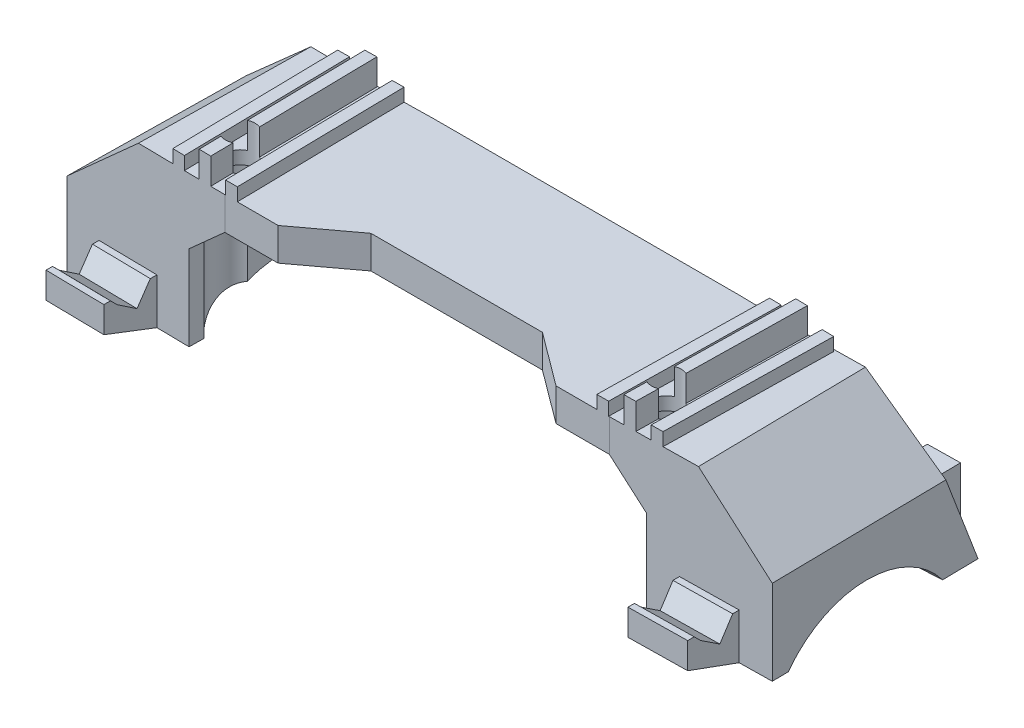
SolidWorks part; units mm, degrees
ref_plane "Front Plane" through (0, 0, 0) normal (0, 0, 1) x (1, 0, 0)
ref_plane "Top Plane" through (0, 0, 0) normal (0, 1, 0) x (1, 0, 0)
ref_plane "Right Plane" through (0, 0, 0) normal (1, 0, 0) x (0, 0, -1)
sketch "Sketch1" plane through (0, 0, 0) normal (0, 1, 0) x (1, 0, 0)
  line L0 (-41.9971, 0) -> (-23, 0.3316)
  line L1 (-23, 0.3316) -> (-23.4773, 27.6774)
  line L2 (-23.4773, 27.6774) -> (-42.4744, 27.3458)
  line L3 (-42.4744, 27.3458) -> (-41.9971, 0)
  line L4 (0, 0) -> (-41.9971, 0) construction
  dimension "D1" = 1
  dimension "D2" = 19
  dimension "D3" = 27.35
  dimension "D4" = 23
extrude "Boss-Extrude1" add sketch "Sketch1" against normal blind 5
sketch "Sketch2" plane through (0, 0, 0) normal (0, 1, 0) x (1, 0, 0)
  line L0 (-33.3984, 0.1501) -> (-33.8757, 27.4959)
  line L1 (-41.9971, 0) -> (-23, 0.3316) construction
  line L2 (-23.4773, 27.6774) -> (-42.4744, 27.3458) construction
  line L3 (-33.8757, 27.4959) -> (-32.076, 27.5273)
  line L4 (-32.076, 27.5273) -> (-31.5987, 0.1815)
  line L5 (-31.5987, 0.1815) -> (-33.3984, 0.1501)
  point P6 (-32.4986, 0.1658)
  dimension "D1" = 1.8
  dimension "D2" = 0.9
extrude "Boss-Extrude2" add sketch "Sketch2" along normal blind 4
sketch "Sketch3" plane through (0, 0, 0) normal (0, 1, 0) x (1, 0, 0)
  line L0 (-37.9751, 27.4244) -> (-36.1754, 27.4558)
  line L1 (-33.8757, 27.4959) -> (-42.4744, 27.3458) construction
  line L2 (-36.1754, 27.4558) -> (-35.6981, 0.11)
  line L3 (-41.9971, 0) -> (-33.3984, 0.1501) construction
  line L4 (-35.6981, 0.11) -> (-37.4978, 0.0785)
  line L5 (-37.4978, 0.0785) -> (-37.9751, 27.4244)
  line L6 (-33.8757, 27.4959) -> (-33.3984, 0.1501) construction
  dimension "D1" = 1.8
  dimension "D2" = 2.3
extrude "Boss-Extrude3" add sketch "Sketch3" along normal blind 2
sketch "Sketch4" plane through (0, 0, 0) normal (0, 1, 0) x (1, 0, 0)
  line L0 (-29.7764, 27.5675) -> (-27.9766, 27.5989)
  line L1 (-23.4773, 27.6774) -> (-32.076, 27.5273) construction
  line L2 (-27.9766, 27.5989) -> (-27.4993, 0.2531)
  line L3 (-31.5987, 0.1815) -> (-23, 0.3316) construction
  line L4 (-27.4993, 0.2531) -> (-29.299, 0.2216)
  line L5 (-29.299, 0.2216) -> (-29.7764, 27.5675)
  line L6 (-31.5987, 0.1815) -> (-32.076, 27.5273) construction
  dimension "D1" = 2.3
  dimension "D2" = 1.8
extrude "Boss-Extrude4" add sketch "Sketch4" along normal blind 2
sketch "Sketch7" plane through (0, 0, 0) normal (0, 1, 0) x (1, 0, 0)
  line L0 (23, 0.3316) -> (41.9971, 0)
  line L1 (41.9971, 0) -> (42.4744, 27.3458)
  line L2 (42.4744, 27.3458) -> (23.4773, 27.6774)
  line L3 (23.4773, 27.6774) -> (23, 0.3316)
  line L4 (0, 0) -> (41.9971, 0) construction
  line L5 (41.9971, 0) -> (23.0236, -1.3184) construction
  dimension "D1" = 23
  dimension "D2" = 1
  dimension "D3" = 19
  dimension "D4" = 27.35
extrude "Boss-Extrude5" add sketch "Sketch7" against normal blind 5 separate body
sketch "Sketch8" plane through (0, 0, 0) normal (0, -1, 0) x (-1, 0, 0)
  line L0 (-31.5987, 0.1815) -> (-32.076, 27.5273)
  line L1 (-23, 0.3316) -> (-41.9971, 0) construction
  line L2 (-42.4744, 27.3458) -> (-23.4773, 27.6774) construction
  line L3 (-32.076, 27.5273) -> (-33.8757, 27.4959)
  line L4 (-33.8757, 27.4959) -> (-33.3984, 0.1501)
  line L5 (-33.3984, 0.1501) -> (-31.5987, 0.1815)
  point P8 (-32.4986, 0.1658)
  dimension "D1" = 1.8
  dimension "D2" = 0.9
extrude "Boss-Extrude6" add sketch "Sketch8" against normal blind 4
sketch "Sketch9" plane through (0, 0, 0) normal (0, -1, 0) x (-1, 0, 0)
  line L0 (-37.4978, 0.0785) -> (-37.9751, 27.4244)
  line L1 (-23, 0.3316) -> (-41.9971, 0) construction
  line L2 (-37.9751, 27.4244) -> (-36.1754, 27.4558)
  line L3 (-42.4744, 27.3458) -> (-23.4773, 27.6774) construction
  line L4 (-36.1754, 27.4558) -> (-35.6981, 0.11)
  line L5 (-35.6981, 0.11) -> (-37.4978, 0.0785)
  line L8 (-33.8757, 27.4959) -> (-33.3984, 0.1501) construction
  dimension "D1" = 1.8
  dimension "D2" = 2.3
extrude "Boss-Extrude7" add sketch "Sketch9" against normal blind 2
sketch "Sketch10" plane through (0, 0, 0) normal (0, -1, 0) x (-1, 0, 0)
  line L0 (-27.4993, 0.2531) -> (-27.9766, 27.5989)
  line L1 (-23, 0.3316) -> (-41.9971, 0) construction
  line L2 (-42.4744, 27.3458) -> (-23.4773, 27.6774) construction
  line L3 (-27.9766, 27.5989) -> (-29.7764, 27.5675)
  line L4 (-29.7764, 27.5675) -> (-29.299, 0.2216)
  line L5 (-29.299, 0.2216) -> (-27.4993, 0.2531)
  line L7 (-31.5987, 0.1815) -> (-32.076, 27.5273) construction
  dimension "D1" = 2.3
  dimension "D2" = 1.8
extrude "Boss-Extrude8" add sketch "Sketch10" against normal blind 2
sketch "Sketch13" plane through (0, 0, 0) normal (0, 1, 0) x (1, 0, 0)
  line L0 (23, 0.3316) -> (27.4993, 0.2531) construction
  line L1 (-23, 0.3316) -> (-23.4773, 27.6774) construction
  line L2 (23.4773, 27.6774) -> (23, 0.3316) construction
  line L3 (23, 0.3316) -> (23.4773, 27.6774)
  line L4 (23.4773, 27.6774) -> (-23.4773, 27.6774)
  line L5 (-23.4773, 27.6774) -> (-23, 0.3316)
  line L6 (23.4773, 27.6774) -> (23, 0.3316) construction
  line L7 (-23, 0.3316) -> (-13.1267, 7.6774)
  line L8 (-13.1267, 7.6774) -> (13.1267, 7.6774)
  line L9 (13.1267, 7.6774) -> (23, 0.3316)
  dimension "D1" = 20
  dimension "D2" = 10
  dimension "D3" = 10
extrude "Boss-Extrude9" add sketch "Sketch13" against normal up to surface (5 mm away) up to face at (-32.7372, -5, -13.8387)
ref_plane "Plane1" through (0, -10, 0) normal (0, 1, 0) x (1, 0, 0)
sketch "Sketch14" plane through (0, -10, 0) normal (0, 1, 0) x (1, 0, 0)
  line L0 (-53.9977, 2) -> (-35, 1.7031)
  line L1 (-35, 1.7031) -> (-34.5, 33.6992)
  line L2 (-34.5, 33.6992) -> (-53.4977, 33.9961)
  line L3 (-53.4977, 33.9961) -> (-53.9977, 2)
  line L4 (-53.9977, 2) -> (0, 2) construction
  dimension "D1" = 34.5
  dimension "D2" = 19
  dimension "D3" = 32
  dimension "D4" = 2
  dimension "D5" = 35
extrude "Boss-Extrude10" add sketch "Sketch14" against normal blind 13 separate body
sketch "Sketch51" plane through (0.0181, 0, -1.1559) normal (-0.0156, 0, 0.9999) x (0.9999, 0, 0.0156)
  line L0 (-54.0223, -10) -> (-35.0223, -10)
  line L1 (-35.0223, -10) -> (-35.0223, -11)
  line L2 (-35.0223, -23) -> (-35.0223, -10) construction
  line L3 (-35.0223, -11) -> (-54.0223, -10)
  dimension "D1" = 1
ref_plane "Plane6" through (-0.674, -12.8078, -0.0105) normal (0.0526, 0.9986, 0.0008) x (-0.9985, 0.0526, -0.0156)
ref_plane "Plane7" through (-53.7157, 1.4128, -0.8394) normal (0.9995, -0.0263, 0.0156) x (0.0156, -0.0004, -0.9999)
sketch "Sketch15" plane through (-54.2786, -19.9965, -0.8482) normal (0.9995, -0.0263, 0.0156) x (-0.0156, 0, 0.9999)
  line L0 (-1.156, 2.9955) -> (-1.156, -10) construction
  line L2 (-33.156, -10) -> (-1.156, -10) construction
  circle A0 centre (-15.656, 12) radius 15
  dimension "D1" = 14.5
  dimension "D2" = 22
  dimension "D5" = 30
extrude "Cut-Extrude6" cut sketch "Sketch15" against normal up to surface (19.1907 mm away) contours A0
sketch "Sketch16" plane through (-54.0157, 0, -0.8441) normal (-0.9999, 0, -0.0156) x (-0.0156, 0, 0.9999)
  line L0 (-33.156, -23) -> (-28.156, -10)
  line L1 (-33.156, -10) -> (-1.156, -10) construction
  line L2 (-28.156, -10) -> (-33.156, -10)
  line L3 (-33.156, -10) -> (-33.156, -23)
  dimension "D1" = 5
extrude "Cut-Extrude7" cut sketch "Sketch16" against normal up to surface (19 mm away) up to face at (-34.7578, -17.7503, -17.2012)
sketch "Sketch18" plane through (0, -23, 0) normal (0, -1, 0) x (1, 0, 0)
  line L0 (-46.4282, -38.3862) -> (-46.5688, -29.3873)
  line L2 (-46.5688, -29.3873) -> (-41.5695, -29.3091)
  line L3 (-41.5695, -29.3091) -> (-41.4288, -38.308)
  line L4 (-46.4282, -38.3862) -> (-41.4288, -38.308)
  line L5 (-34.5, -33.6992) -> (-53.4977, -33.9961) construction
  line L8 (-34.5921, -27.8049) -> (-34.5, -33.6992) construction
  dimension "D1" = 4.5
  dimension "D2" = 5
  dimension "D3" = 7
  dimension "D4" = 4.5
extrude "Boss-Extrude12" add sketch "Sketch18" against normal blind 7
sketch "Sketch24" plane through (0, -10, 0) normal (0, 1, 0) x (1, 0, 0)
  line L0 (-48.5764, 28.9186) -> (-48.4983, 33.918)
  line L1 (-34.5781, 28.6998) -> (-53.5758, 28.9967) construction
  line L2 (-46.4985, 33.8867) -> (-53.4977, 33.9961) construction
  line L3 (-48.4983, 33.918) -> (-39.4994, 33.7773)
  line L4 (-34.5, 33.6992) -> (-41.4991, 33.8086) construction
  line L5 (-39.4994, 33.7773) -> (-39.5775, 28.778)
  line L6 (-39.5775, 28.778) -> (-48.5764, 28.9186)
  line L7 (-53.4977, 33.9961) -> (-53.5758, 28.9967) construction
  dimension "D1" = 9
  dimension "D2" = 5
extrude "Cut-Extrude12" cut sketch "Sketch24" against normal up to surface (6 mm away) up to face at (-43.9847, -16, -34.7514)
sketch "Sketch26" plane through (-49.0164, 0, -0.766) normal (0.9999, 0, 0.0156) x (0.0156, 0, -0.9999)
  line L0 (30.4637, -16) -> (37.656, -16) construction
  circle A0 centre (31.156, -16) radius 3
  dimension "D1" = 6
extrude "Cut-Extrude14" cut sketch "Sketch26" along normal up to surface (9 mm away) up to face at (-39.5655, -14, -29.5471)
sketch "Sketch30" plane through (0, -10, 0) normal (0, 1, 0) x (1, 0, 0)
  line L2 (-53.4977, 33.9961) -> (-53.5758, 28.9967) construction
  line L4 (-50.5452, 30.9183) -> (-50.4978, 33.9492)
  line L5 (-50.4978, 33.9492) -> (-46.4988, 33.8867)
  line L9 (-46.5452, 30.9183) -> (-46.4988, 33.8867)
  line L11 (-46.4985, 33.8867) -> (-53.4977, 33.9961) construction
  line L16 (-48.5764, 28.9186) -> (-53.5758, 28.9967) construction
  arc A2 (-46.5452, 30.9183) -> (-50.5452, 30.9183) centre (-48.5452, 30.9183) cw
  dimension "D1" = 2
  dimension "D3" = 5
extrude "Cut-Extrude16" cut sketch "Sketch30" against normal up to surface (13 mm away) up to face at (-44.4581, -23, -3.2)
sketch "Sketch31" plane through (0, -10, 0) normal (0, 1, 0) x (1, 0, 0)
  line L0 (-34.5781, 28.6998) -> (-39.5775, 28.778) construction
  line L1 (-37.5465, 30.7465) -> (-37.4996, 33.7461)
  line L2 (-34.5, 33.6992) -> (-41.4991, 33.8086) construction
  line L3 (-37.4996, 33.7461) -> (-41.4991, 33.8086)
  line L4 (-41.4991, 33.8086) -> (-41.5234, 32.2574) construction
  line L5 (-41.4991, 33.8086) -> (-41.546, 30.809)
  arc A0 (-37.5465, 30.7465) -> (-41.546, 30.809) centre (-39.5463, 30.7777) cw
  dimension "D1" = 2
extrude "Cut-Extrude17" cut sketch "Sketch31" against normal up to surface (13 mm away) up to face at (-44.4581, -23, -3.2)
sketch "Sketch34" plane through (0, -23, 0) normal (0, -1, 0) x (1, 0, 0)
  line L0 (-48.9983, -1.9219) -> (-49.1233, 6.0771)
  line L1 (-53.9977, -2) -> (-35, -1.7031) construction
  line L2 (-49.1233, 6.0771) -> (-40.1244, 6.2178)
  line L3 (-40.1244, 6.2178) -> (-39.9994, -1.7812)
  line L4 (-39.9994, -1.7812) -> (-48.9983, -1.9219)
  line L5 (-53.9586, -4.5031) -> (-53.9977, -2) construction
  dimension "D1" = 8
  dimension "D2" = 9
  dimension "D3" = 5
extrude "Boss-Extrude15" add sketch "Sketch34" against normal blind 7
sketch "Sketch20" plane through (0, -10, 0) normal (0, 1, 0) x (1, 0, 0)
  line L0 (35, 1.7031) -> (53.9977, 2)
  line L1 (53.9977, 2) -> (53.4977, 33.9961)
  line L2 (53.4977, 33.9961) -> (34.5, 33.6992)
  line L3 (34.5, 33.6992) -> (35, 1.7031)
  line L4 (53.9977, 2) -> (0, 2) construction
  dimension "D1" = 19
  dimension "D2" = 32
  dimension "D3" = 2
  dimension "D4" = 34.5
  dimension "D5" = 35
extrude "Boss-Extrude13" add sketch "Sketch20" against normal blind 13 separate body
sketch "Sketch52" plane through (-0.0181, 0, -1.1559) normal (0.0156, 0, 0.9999) x (0.9999, 0, -0.0156)
  line L0 (54.0223, -10) -> (35.0223, -10)
  line L1 (33.067, -10) -> (-33.067, -10) construction
  line L2 (35.0223, -10) -> (35.0223, -11)
  line L3 (35.0223, -23) -> (35.0223, -10) construction
  line L4 (35.0223, -11) -> (54.0223, -10)
  line L5 (54.0223, -23) -> (54.0223, -10) construction
  dimension "D1" = 1
ref_plane "Plane8" through (0.674, -12.8078, -0.0105) normal (0.0526, -0.9986, -0.0008) x (0.9985, 0.0526, -0.0156)
ref_plane "Plane9" through (53.3417, 2.8078, -0.8336) normal (-0.9985, -0.0526, 0.0156) x (-0.0156, 0, -0.9999)
sketch "Sketch21" plane through (54.5413, -19.9862, -0.8523) normal (-0.9985, -0.0526, 0.0156) x (-0.0156, 0, -0.9999)
  line L0 (1.156, -10) -> (33.156, -10) construction
  line L2 (1.156, 2.982) -> (1.156, -10) construction
  circle A0 centre (15.656, 12) radius 15
  dimension "D1" = 30
  dimension "D2" = 22
  dimension "D3" = 14.5
extrude "Cut-Extrude10" cut sketch "Sketch21" against normal up to surface (20.9737 mm away)
sketch "Sketch22" plane through (54.0157, 0, -0.8441) normal (0.9999, 0, -0.0156) x (-0.0156, 0, -0.9999)
  line L0 (33.156, -23) -> (28.156, -10)
  line L1 (33.067, -10) -> (-33.067, -10) construction
  line L2 (28.156, -10) -> (33.156, -10)
  line L3 (33.156, -10) -> (33.156, -23)
  dimension "D1" = 5
extrude "Cut-Extrude11" cut sketch "Sketch22" against normal up to surface (19 mm away) up to face at (34.7578, -17.8349, -17.2012)
sketch "Sketch37" plane through (-49.0164, 0, -0.766) normal (-0.9999, 0, -0.0156) x (-0.0156, 0, 0.9999)
  line L0 (-1.156, -23) -> (6.844, -20)
  line L1 (6.844, -16) -> (6.844, -23) construction
  line L2 (6.844, -20) -> (6.844, -23)
  line L3 (6.844, -23) -> (-1.156, -23)
  dimension "D1" = 3
extrude "Cut-Extrude21" cut sketch "Sketch37" against normal up to surface (9 mm away) up to face at (-40.0463, -18.625, 1.2184)
sketch "Sketch38" plane through (-49.0164, 0, -0.766) normal (-0.9999, 0, -0.0156) x (-0.0156, 0, 0.9999)
  line L0 (5.844, -16) -> (4.844, -17)
  line L1 (6.844, -16) -> (-1.156, -16) construction
  line L2 (4.844, -17) -> (1.844, -19)
  line L3 (1.844, -19) -> (-0.156, -16)
  line L4 (-0.156, -16) -> (5.844, -16)
  line L5 (-1.156, -16) -> (-1.156, -23) construction
  line L6 (-1.156, -23) -> (-1.156, -10) construction
  line L7 (6.844, -16) -> (6.844, -20) construction
  dimension "D1" = 3
  dimension "D2" = 3
  dimension "D3" = 1
  dimension "D4" = 1
  dimension "D5" = 1
  dimension "D6" = 2
extrude "Cut-Extrude22" cut sketch "Sketch38" against normal up to surface (9 mm away) up to face at (-40.0775, -17.5, 3.2181)
sketch "Sketch23" plane through (0, -23, 0) normal (0, -1, 0) x (1, 0, 0)
  line L0 (41.5695, -29.3091) -> (46.5688, -29.3873)
  line L2 (46.5688, -29.3873) -> (46.4282, -38.3862)
  line L3 (46.4282, -38.3862) -> (41.4288, -38.308)
  line L4 (41.4288, -38.308) -> (41.5695, -29.3091)
  line L5 (53.5838, -28.4833) -> (53.4977, -33.9961) construction
  line L6 (53.4977, -33.9961) -> (34.5, -33.6992) construction
  dimension "D1" = 4.5
  dimension "D2" = 5
  dimension "D3" = 7
  dimension "D4" = 4.5
extrude "Boss-Extrude14" add sketch "Sketch23" against normal blind 7
sketch "Sketch25" plane through (0, -10, 0) normal (0, 1, 0) x (1, 0, 0)
  line L0 (39.5775, 28.778) -> (48.5764, 28.9186)
  line L1 (34.5781, 28.6998) -> (53.5758, 28.9967) construction
  line L2 (48.5764, 28.9186) -> (48.4983, 33.918)
  line L3 (53.4977, 33.9961) -> (46.4985, 33.8867) construction
  line L4 (48.4983, 33.918) -> (39.4994, 33.7773)
  line L5 (41.4991, 33.8086) -> (34.5, 33.6992) construction
  line L6 (39.4994, 33.7773) -> (39.5775, 28.778)
  line L7 (34.5781, 28.6998) -> (34.5, 33.6992) construction
  dimension "D1" = 9
  dimension "D2" = 5
extrude "Cut-Extrude13" cut sketch "Sketch25" against normal up to surface (6 mm away) up to face at (43.9847, -16, -34.7514)
sketch "Sketch27" plane through (49.0164, 0, -0.766) normal (-0.9999, 0, 0.0156) x (0.0156, 0, 0.9999)
  line L0 (-37.656, -16) -> (-30.4637, -16) construction
  circle A0 centre (-31.156, -16) radius 3
  dimension "D1" = 6
extrude "Cut-Extrude15" cut sketch "Sketch27" along normal up to surface (9 mm away) up to face at (39.5655, -14, -29.5471)
sketch "Sketch32" plane through (0, -10, 0) normal (0, 1, 0) x (1, 0, 0)
  line L0 (46.5454, 30.8871) -> (46.4985, 33.8867)
  line L1 (53.4977, 33.9961) -> (46.4985, 33.8867) construction
  line L2 (46.4985, 33.8867) -> (50.498, 33.9492)
  line L3 (50.498, 33.9492) -> (50.5449, 30.9496)
  line L4 (48.5764, 28.9186) -> (53.5758, 28.9967) construction
  line L5 (46.5228, 32.3355) -> (46.4829, 34.8866) construction
  arc A0 (50.5449, 30.9496) -> (46.5454, 30.8871) centre (48.5452, 30.9183) cw
  dimension "D1" = 2
extrude "Cut-Extrude18" cut sketch "Sketch32" against normal up to surface (13 mm away) up to face at (44.434, -23, -3.31)
sketch "Sketch33" plane through (0, -10, 0) normal (0, 1, 0) x (1, 0, 0)
  line L0 (37.5465, 30.7465) -> (37.4996, 33.7461)
  line L1 (41.4991, 33.8086) -> (34.5, 33.6992) construction
  line L2 (37.4996, 33.7461) -> (41.4991, 33.8086)
  line L3 (41.4991, 33.8086) -> (41.546, 30.809)
  line L4 (41.5234, 32.2574) -> (41.4991, 33.8086) construction
  line L5 (34.5781, 28.6998) -> (39.5775, 28.778) construction
  arc A0 (41.546, 30.809) -> (37.5465, 30.7465) centre (39.5463, 30.7777) cw
  dimension "D1" = 2
extrude "Cut-Extrude19" cut sketch "Sketch33" against normal up to surface (13 mm away) up to face at (44.434, -23, -3.31)
sketch "Sketch35" plane through (0, -23, 0) normal (0, -1, 0) x (1, 0, 0)
  line L0 (39.9994, -1.7813) -> (40.1244, 6.2178)
  line L1 (35, -1.7031) -> (53.9977, -2) construction
  line L2 (40.1244, 6.2178) -> (49.1233, 6.0771)
  line L3 (49.1233, 6.0771) -> (48.9983, -1.9219)
  line L4 (48.9983, -1.9219) -> (39.9994, -1.7813)
  line L5 (53.9977, -2) -> (53.9584, -4.5132) construction
  dimension "D1" = 9
  dimension "D2" = 8
  dimension "D3" = 5
extrude "Boss-Extrude16" add sketch "Sketch35" against normal blind 7
sketch "Sketch36" plane through (49.0164, 0, -0.766) normal (0.9999, 0, -0.0156) x (-0.0156, 0, -0.9999)
  line L0 (1.156, -23) -> (-6.844, -20)
  line L1 (-6.844, -16) -> (-6.844, -23) construction
  line L2 (-6.844, -20) -> (-6.844, -23)
  line L3 (-6.844, -23) -> (1.156, -23)
  dimension "D1" = 3
extrude "Cut-Extrude20" cut sketch "Sketch36" against normal up to surface (9 mm away) up to face at (40.0775, -18.625, 3.2181)
sketch "Sketch39" plane through (49.0164, 0, -0.766) normal (0.9999, 0, -0.0156) x (-0.0156, 0, -0.9999)
  line L0 (-5.844, -16) -> (-4.844, -17)
  line L1 (1.156, -16) -> (-6.844, -16) construction
  line L2 (-4.844, -17) -> (-1.844, -19)
  line L3 (-1.844, -19) -> (0.156, -16)
  line L4 (-5.844, -16) -> (0.156, -16)
  line L5 (1.156, -23) -> (1.156, -10) construction
  line L6 (1.156, -16) -> (1.156, -23) construction
  line L7 (-6.844, -16) -> (-6.844, -20) construction
  dimension "D1" = 1
  dimension "D2" = 1
  dimension "D3" = 3
  dimension "D4" = 3
  dimension "D5" = 2
  dimension "D6" = 1
extrude "Cut-Extrude23" cut sketch "Sketch39" against normal up to surface (9 mm away) up to face at (40.0463, -18.25, 1.2184)
sketch "Sketch41" plane through (-0.465, 0, -1.1634) normal (0.0156, 0, -0.9999) x (-0.9999, 0, -0.0156)
  line L0 (42.4134, 0) -> (53.5393, -10)
  line L1 (37.9159, 0) -> (42.4134, 0) construction
  line L2 (42.4134, -5) -> (42.4134, 0) construction
  line L5 (32.5839, -10) -> (-33.5501, -10) construction
  line L6 (53.5393, -10) -> (34.5393, -10)
  line L7 (34.5393, -10) -> (28.9764, -5)
  line L8 (23.4238, -5) -> (42.4134, -5) construction
  line L9 (28.9764, -5) -> (28.9764, 0)
  line L10 (28.9764, 0) -> (42.4134, 0)
  line L11 (34.5393, -23) -> (34.5393, -10) construction
extrude "Boss-Extrude17" add sketch "Sketch41" along normal up to surface (27 mm away) up to face at (-44.077, -13, -28.8483)
sketch "Sketch42" plane through (0.465, 0, -1.1634) normal (-0.0156, 0, -0.9999) x (-0.9999, 0, 0.0156)
  line L0 (-42.4134, 0) -> (-53.5393, -10)
  line L1 (33.5501, -10) -> (-32.5839, -10) construction
  line L2 (-53.5393, -10) -> (-34.5393, -10)
  line L3 (-34.5393, -10) -> (-28.9764, -5)
  line L4 (-42.4134, -5) -> (-23.4238, -5) construction
  line L5 (-28.9764, -5) -> (-28.9764, 0)
  line L6 (-28.9764, 0) -> (-42.4134, 0)
  line L7 (-34.5393, -10) -> (-34.5393, -23) construction
  line L8 (-53.5393, -23) -> (-53.5393, -10) construction
extrude "Boss-Extrude18" add sketch "Sketch42" along normal up to surface (27 mm away) up to face at (44.077, -13, -28.8483)
sketch "Sketch48" plane through (-54.0157, 0, -0.8441) normal (-0.9999, 0, -0.0156) x (-0.0156, 0, 0.9999)
  line L0 (-28.156, -10) -> (-28.156, 0)
  line L1 (-28.156, 0) -> (-27.1584, 0)
  line L2 (-27.1584, 0) -> (-28.156, -10)
extrude "Cut-Extrude27" cut sketch "Sketch48" against normal up to surface (24.5629 mm away) contours L0 L1 L2 up to face at (-29.024, -2.5, -28.0967)
sketch "Sketch49" plane through (54.0157, 0, -0.8441) normal (0.9999, 0, -0.0156) x (-0.0156, 0, -0.9999)
  line L1 (33.067, -10) -> (-33.067, -10) construction
  line L2 (28.156, -10) -> (33.156, -23) construction
  line L3 (28.156, -10) -> (28.156, 0)
  line L4 (28.156, 0) -> (27.1235, 0)
  line L5 (27.1235, 0) -> (28.156, -10)
extrude "Cut-Extrude28" cut sketch "Sketch49" against normal up to surface (24.5629 mm away) up to face at (29.024, -2.5, -28.0967)
sketch "Sketch47" plane through (0, -5, 0) normal (0, -1, 0) x (1, 0, 0)
  line L0 (-44.4988, -1.8516) -> (-29.4378, -1.6162)
  line L1 (-39.9994, -1.7812) -> (-48.9983, -1.9219) construction
  line L2 (39.9994, -1.7813) -> (48.9983, -1.9219) construction
  line L3 (44.4988, -1.8516) -> (44.4988, 3.1484)
  line L4 (44.4988, 3.1484) -> (-44.4988, 3.1484)
  line L5 (-44.4988, 3.1484) -> (-44.4988, -1.8516)
  line L6 (-29.4378, -1.6162) -> (29.4378, -1.6162)
  line L7 (29.4378, -1.6162) -> (44.4988, -1.8516)
  dimension "D1" = 5
extrude "Cut-Extrude26" cut sketch "Sketch47" against normal up to surface (9 mm away) up to face at (-32.7372, 4, -13.8387)
sketch "Sketch5" plane through (0, 4, 0) normal (0, 1, 0) x (1, 0, 0)
  line L2 (-33.8757, 27.4959) -> (-33.4251, 1.6785) construction
  line L4 (-32.076, 27.5273) -> (-33.8757, 27.4959) construction
  circle A0 centre (-32.6207, 7.1647) radius 2.25
  dimension "D3" = 4.5
  dimension "D1" = 20.35
  dimension "D2" = 0.9
extrude "Cut-Extrude1" cut sketch "Sketch5" against normal up to surface (9 mm away)
sketch "Sketch6" plane through (0, -5, 0) normal (0, -1, 0) x (1, 0, 0)
  circle A0 centre (-32.6207, -7.1647) radius 4
  circle A1 centre (-32.6207, -7.1647) radius 2.25 construction
  dimension "D1" = 8
extrude "Cut-Extrude2" cut sketch "Sketch6" against normal offset from surface 6 and the other way through all up to face at (-32.5539, 4, -3.3367)
sketch "Sketch11" plane through (0, 4, 0) normal (0, 1, 0) x (1, 0, 0)
  line L2 (33.8757, 27.4959) -> (33.4251, 1.6785) construction
  line L3 (32.076, 27.5273) -> (33.8757, 27.4959) construction
  circle A0 centre (32.6207, 7.1647) radius 2.25
  dimension "D1" = 4.5
  dimension "D2" = 20.35
  dimension "D3" = 0.9
extrude "Cut-Extrude3" cut sketch "Sketch11" against normal up to surface (9 mm away) up to face at (-4.8311, -5, -12.2126)
sketch "Sketch12" plane through (0, -5, 0) normal (0, 1, 0) x (-1, 0, 0)
  circle A0 centre (-32.6207, -7.1647) radius 4
  dimension "D1" = 8
extrude "Cut-Extrude5" cut sketch "Sketch12" along normal offset from surface 6 and the other way through all up to face at (32.5539, 4, -3.3367)
